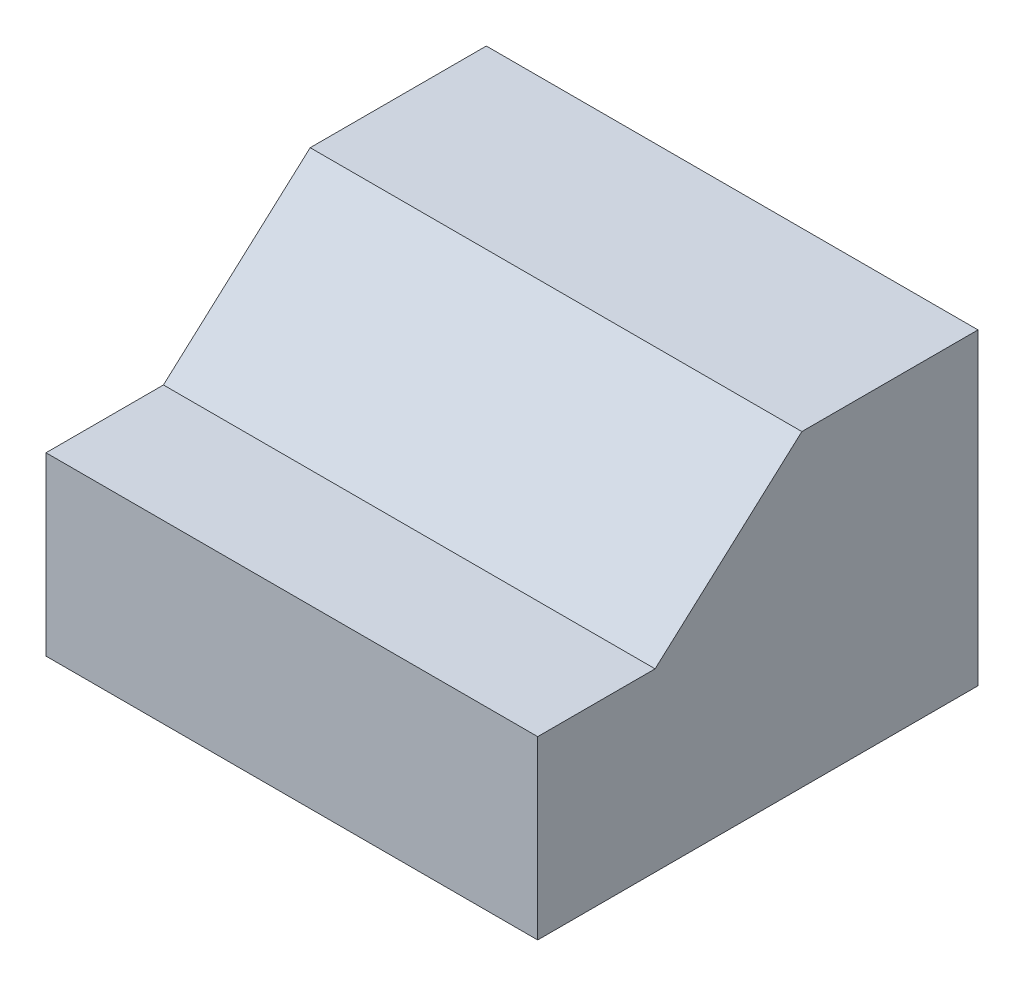
SolidWorks part; units mm, degrees
ref_plane "Front Plane" through (0, 0, 0) normal (0, 0, 1) x (1, 0, 0)
ref_plane "Top Plane" through (0, 0, 0) normal (0, 1, 0) x (1, 0, 0)
ref_plane "Right Plane" through (0, 0, 0) normal (1, 0, 0) x (0, 0, -1)
sketch "Sketch1" plane through (0, 0, 0) normal (1, 0, 0) x (0, 0, -1)
  line L0 (0, 0) -> (-406.4, 0)
  line L1 (-406.4, 0) -> (-406.4, -609.6)
  line L2 (-406.4, -609.6) -> (1117.6, -609.6)
  line L3 (1117.6, -609.6) -> (1117.6, 457.2)
  line L4 (1117.6, 457.2) -> (508, 457.2)
  line L5 (508, 457.2) -> (0, 0)
  dimension "D1" = 457.2
  dimension "D2" = 406.4
  dimension "D3" = 609.6
  dimension "D4" = 609.6
  dimension "D5" = 1524
extrude "Boss-Extrude1" add sketch "Sketch1" along normal mid plane 1701.8
